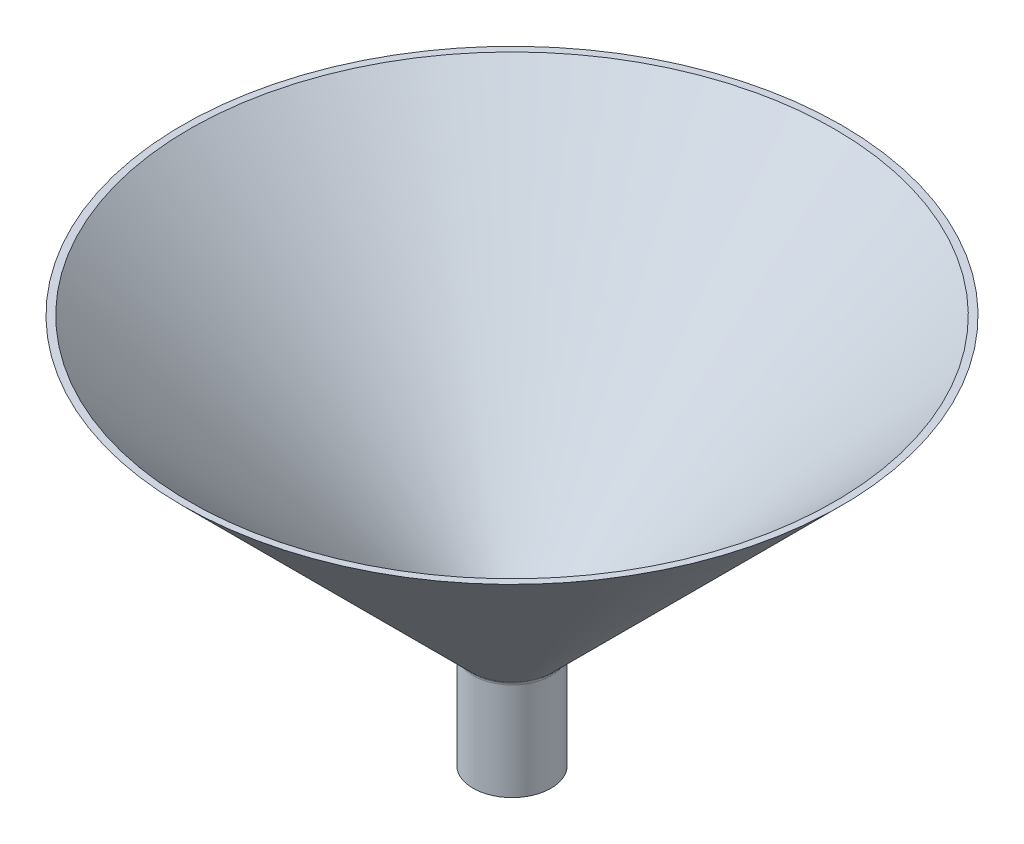
SolidWorks part; units mm, degrees
ref_plane "Front Plane" through (0, 0, 0) normal (0, 0, 1) x (1, 0, 0)
ref_plane "Top Plane" through (0, 0, 0) normal (0, 1, 0) x (1, 0, 0)
ref_plane "Right Plane" through (0, 0, 0) normal (1, 0, 0) x (0, 0, -1)
sketch "Sketch2" plane through (0, 0, 0) normal (0, 0, 1) x (1, 0, 0)
  line L1 (-10.5, 0) -> (-10.5, 30)
  line L4 (-11.3787, 32.1213) -> (-99.2574, 120)
  line L5 (-11.3787, 32.1213) -> (-11.3791, 32.1217) construction
  line L6 (-12, 0) -> (-12, 30)
  line L7 (-12.4393, 31.0607) -> (-12.4397, 31.061)
  line L8 (-12.4393, 31.0607) -> (-101.3787, 120)
  line L9 (-12, -1.5) -> (-12, 30) construction
  line L10 (-9.25, 0) -> (-10.5, 0) construction
  line L11 (-9.25, -1.5) -> (-12, -1.5) construction
  line L12 (-10.5, 0) -> (-12, 0)
  line L13 (-101.3787, 120) -> (-99.2574, 120)
  line L14 (-11.3787, 32.1213) -> (-100.318, 121.0607) construction
  line L15 (0, 0) -> (0, 14.4174) construction
  arc A0 (-11.3787, 32.1213) -> (-10.5, 30) centre (-13.5, 30) cw
  arc A1 (-12.4393, 31.0607) -> (-12, 30) centre (-13.5, 30) cw
  arc A2 (-12.4393, 31.0607) -> (-12, 30) centre (-13.5, 30) cw construction
  dimension "D2" = 3
  dimension "D1" = 1.5
  dimension "D4" = 10.5
  dimension "D3" = 90
  dimension "D5" = 30
  dimension "D6" = 135
revolve "Revolve1" add sketch "Sketch2" angle 360 about L15
sketch "Sketch3" plane through (0, 0, 0) normal (1, 0, 0) x (0, 0, -1)
  line L0 (12, 0) -> (12, 30) construction
  circle A0 centre (25, 20) radius 20.5
  point P2 (12, 15)
  point P3 (0, 0)
  point P8 (0, 0)
  point P9 (25, 11.2267)
  dimension "D1" = 41
  dimension "D2" = 25
  dimension "D3" = 5
extrude "Cut-Extrude1" cut sketch "Sketch3" against normal mid plane 5
